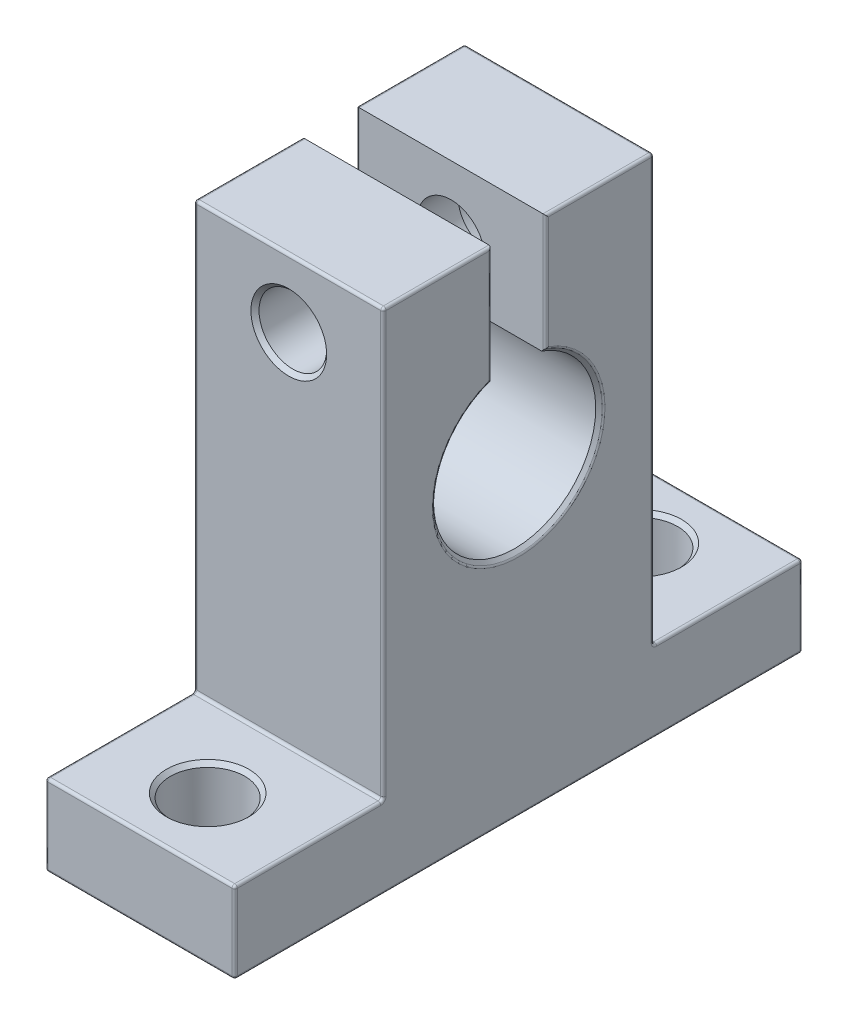
SolidWorks part; units mm, degrees
material "АМг 2 ГОСТ 4784-97"
ref_plane "Front Plane" through (0, 0, 0) normal (0, 0, 1) x (1, 0, 0)
ref_plane "Top Plane" through (0, 0, 0) normal (0, 1, 0) x (1, 0, 0)
ref_plane "Right Plane" through (0, 0, 0) normal (1, 0, 0) x (0, 0, -1)
sketch "Sketch1" plane through (0, 0, 0) normal (1, 0, 0) x (0, 0, -1)
  line L0 (-21, 0) -> (21, 0)
  line L1 (21, 0) -> (21, 6)
  line L2 (21, 6) -> (10, 6)
  line L3 (10, 6) -> (10, 37.5)
  line L4 (10, 37.5) -> (2, 37.5)
  line L5 (-10, 37.5) -> (-10, 6)
  line L6 (-10, 6) -> (-21, 6)
  line L7 (-21, 6) -> (-21, 0)
  line L8 (0, 0) -> (0, 42.202) construction
  line L9 (2, 28.6569) -> (2, 37.5)
  line L10 (-2, 28.6569) -> (-2, 37.5)
  line L14 (-2, 37.5) -> (-10, 37.5)
  arc A0 (-2, 28.6569) -> (2, 28.6569) centre (0, 23) ccw
  dimension "D8" = 12
  dimension "D1" = 42
  dimension "D2" = 37.5
  dimension "D3" = 21
  dimension "D4" = 20
  dimension "D5" = 10
  dimension "D6" = 6
  dimension "D7" = 6
  dimension "D9" = 23
  dimension "D10" = 4
extrude "Boss-Extrude1" add sketch "Sketch1" along normal mid plane 14
sketch "Sketch2" plane through (0, 6, 0) normal (0, 1, 0) x (1, 0, 0)
  line L0 (6.2165, 0) -> (-7.7404, 0) construction
  line L1 (7, -10) -> (7, -21) construction
  circle A0 centre (0, 16) radius 2.75
  circle A1 centre (0, -16) radius 2.75
  dimension "D3" = 7
  dimension "D1" = 32
  dimension "D2" = 5.5
extrude "Cut-Extrude1" cut sketch "Sketch2" against normal through all
sketch "Sketch3" plane through (0, 0, -10) normal (0, 0, -1) x (-1, 0, 0)
  line L0 (-7, 37.5) -> (7, 37.5) construction
  circle A0 centre (0, 32.5) radius 2.5
  point P2 (0, 37.5)
  dimension "D1" = 5
  dimension "D2" = 5
extrude "Cut-Extrude2" cut sketch "Sketch3" against normal through all
sketch "Sketch4" plane through (0, 0, -10) normal (0, 0, -1) x (-1, 0, 0)
  circle A0 centre (0, 32.5) radius 4
  dimension "D1" = 8
extrude "Cut-Extrude3" cut sketch "Sketch4" against normal blind 5
chamfer "Фаска1" distance 0.3 angle 45 7 edges at (0, 0, -13.25) (0, 0, 18.75) (0, 6, 18.75) (0, 6, -13.25) (-4, 32.5, -10) (0, 35, 10) (7, 17, 0)
fillet "Скругление1" radius 0.2 32 edges at (-7, 0, 0) (-7, 3, -21) (-7, 6, -15.5) (-7, 21.75, -10) (-7, 37.5, -6) (-7, 33.0784, -2) (-7, 17, 0) (-7, 33.0784, 2) (-7, 37.5, 6) (-7, 21.75, 10) (-7, 6, 15.5) (-7, 3, 21) (7, 37.5, -6) (7, 21.75, -10) (7, 6, -15.5) (7, 3, -21) (7, 0, 0) (7, 3, 21) (7, 6, 15.5) (7, 21.75, 10) (7, 37.5, 6) (7, 33.2371, 2) (7, 16.7, 0) (7, 33.2371, -2) (0, 0, 21) (0, 6, 21) (0, 6, 10) (0, 37.5, 10) (0, 0, -21) (0, 6, -21) (0, 6, -10) (0, 37.5, -10)
